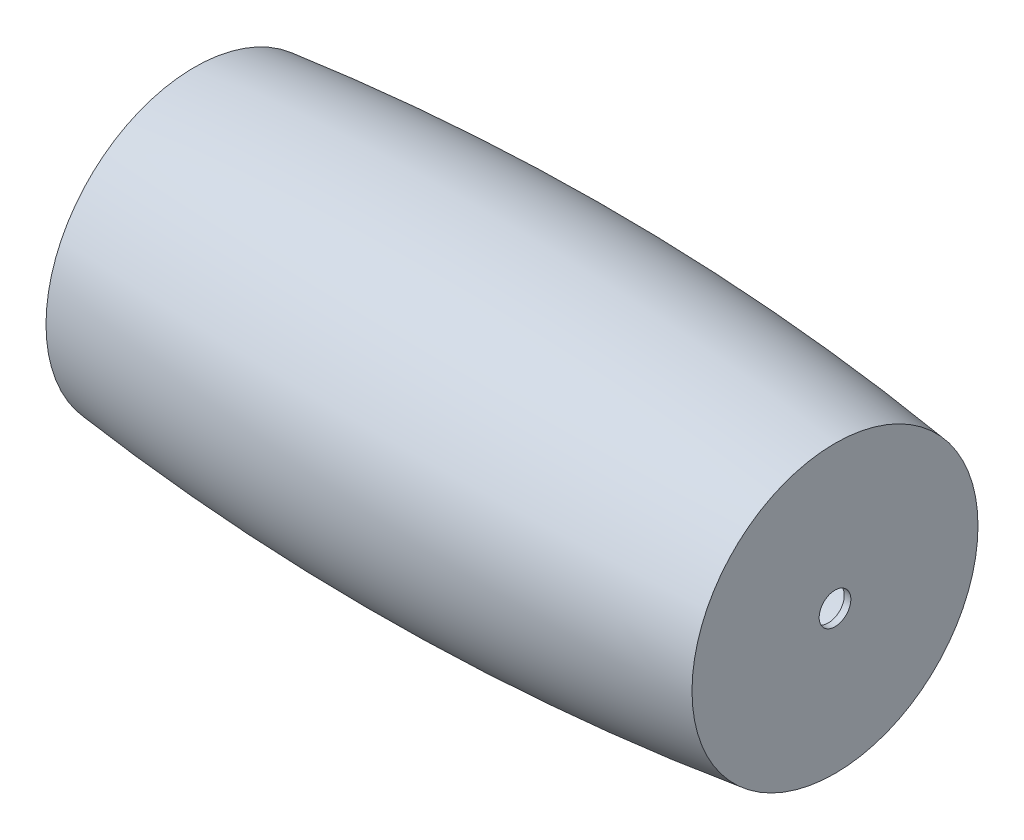
SolidWorks part; units mm, degrees
ref_plane "Спереди" through (0, 0, 0) normal (0, 0, 1) x (1, 0, 0)
ref_plane "Сверху" through (0, 0, 0) normal (0, 1, 0) x (1, 0, 0)
ref_plane "Справа" through (0, 0, 0) normal (1, 0, 0) x (0, 0, -1)
sketch "Эскиз1" plane through (0, 0, 0) normal (0, 0, 1) x (1, 0, 0)
  line L0 (0, 21.9204) -> (0, 31.9825)
  line L1 (970, -193.0175) -> (970, 23.565)
  line L2 (960, -193.0175) -> (970, -193.0175)
  line L3 (960, -183.0175) -> (960, 14.7631) construction
  line L4 (960, -193.0175) -> (960, 14.7631)
  line L5 (0, -193.0175) -> (0, 31.9825) construction
  line L6 (10, -183.0175) -> (10, 23.0252) construction
  line L7 (10, -183.0175) -> (960, -183.0175) construction
  line L8 (0, -193.0175) -> (970, -193.0175) construction
  arc A0 (0, 31.9825) -> (970, 23.565) centre (450, -4005.5175) cw
  arc A1 (0, 21.9204) -> (960, 14.7631) centre (450, -4005.5175) cw
  arc A2 (10, 23.0252) -> (960, 14.7631) centre (450, -4005.5175) cw construction
  dimension "D2" = 970
  dimension "D4" = 10
revolve "Повернуть1" add sketch "Эскиз1" angle 360 about L2
sketch "Эскиз2" plane through (0, 0, 0) normal (-1, 0, 0) x (0, 0, 1)
  circle A0 centre (0, -193.0175) radius 24
  dimension "D1" = 48
extrude "Вырез-Вытянуть1" cut sketch "Эскиз2" against normal through all
